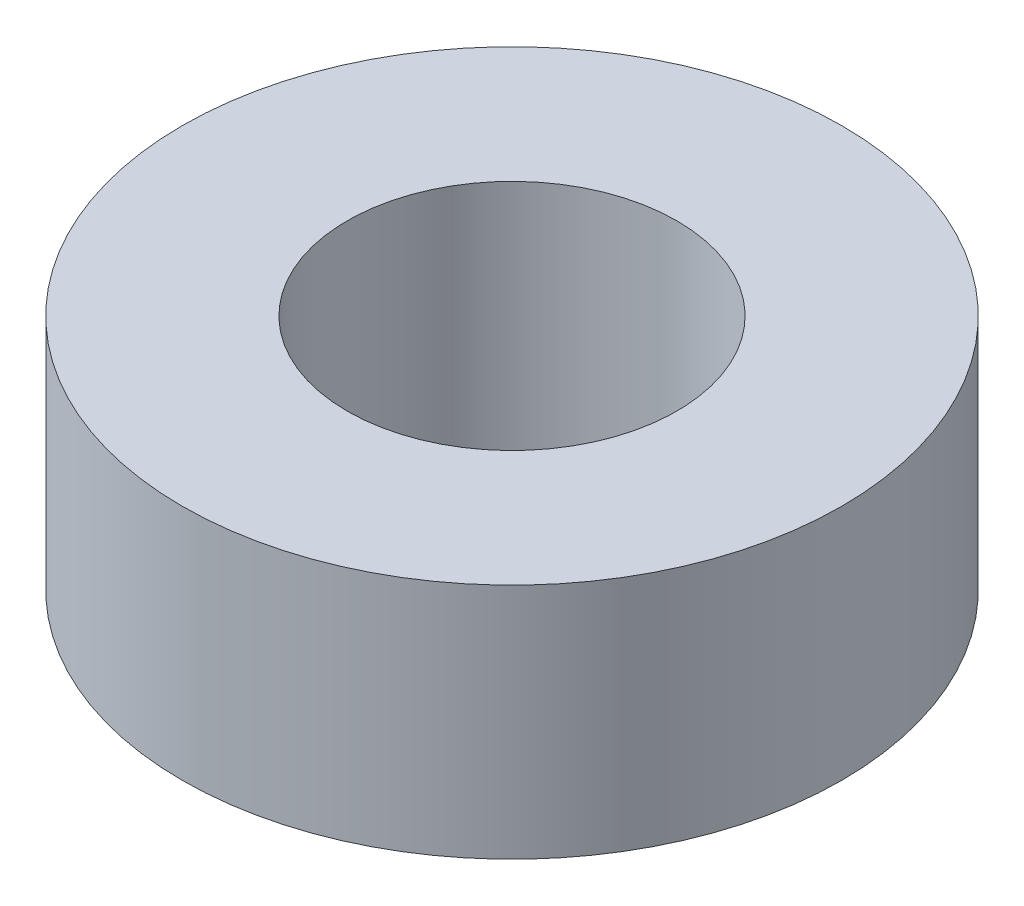
SolidWorks part; units mm, degrees
ref_plane "Front Plane" through (0, 0, 0) normal (0, 0, 1) x (1, 0, 0)
ref_plane "Top Plane" through (0, 0, 0) normal (0, 1, 0) x (1, 0, 0)
ref_plane "Right Plane" through (0, 0, 0) normal (1, 0, 0) x (0, 0, -1)
sketch "Sketch1" plane through (0, 0, 0) normal (0, 1, 0) x (1, 0, 0)
  circle A0 centre (0, 0) radius 12.5
  circle A1 centre (0, 0) radius 6.25
  dimension "D1" = 25
  dimension "D2" = 12.5
extrude "Boss-Extrude1" add sketch "Sketch1" along normal blind 9
